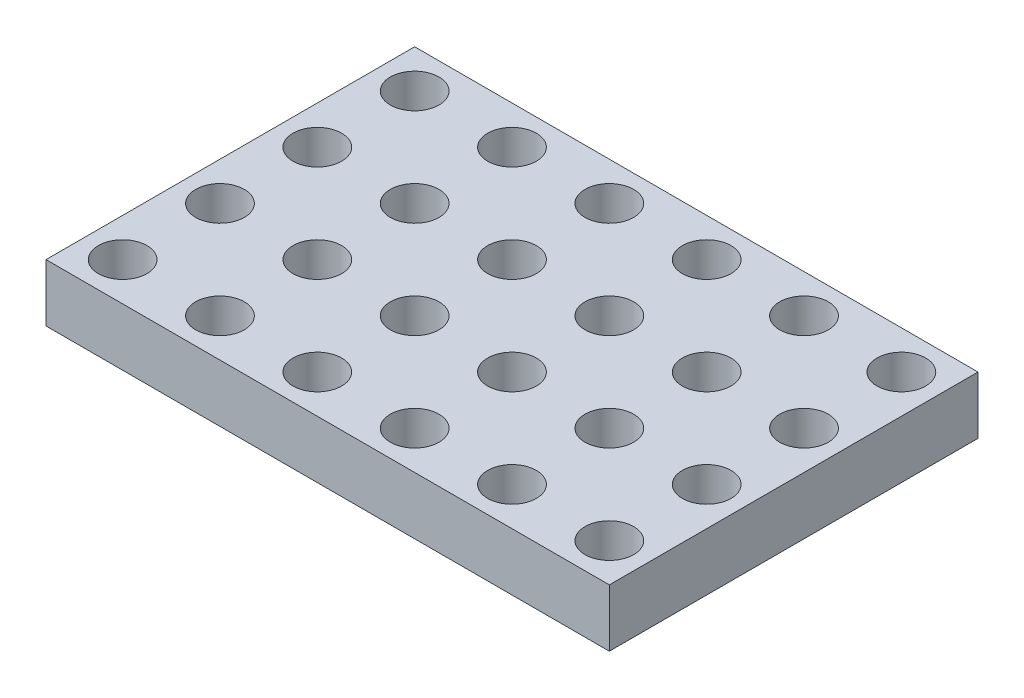
SolidWorks part; units mm, degrees
ref_plane "Front Plane" through (0, 0, 0) normal (0, 0, 1) x (1, 0, 0)
ref_plane "Top Plane" through (0, 0, 0) normal (0, 1, 0) x (1, 0, 0)
ref_plane "Right Plane" through (0, 0, 0) normal (1, 0, 0) x (0, 0, -1)
sketch "Sketch1" plane through (0, 0, 0) normal (0, 1, 0) x (1, 0, 0)
  line L0 (0, 10.1825) -> (0, -8.1829) construction
  line L1 (7.35, -4.81) -> (-7.35, -4.81)
  line L2 (7.35, -4.81) -> (7.35, 4.81)
  line L3 (7.35, 4.81) -> (-7.35, 4.81)
  line L4 (-7.35, -4.81) -> (-7.35, 4.81)
  line L5 (7.35, -4.81) -> (-7.35, 4.81) construction
  line L6 (7.35, 4.81) -> (-7.35, -4.81) construction
  line L7 (12.6443, 0) -> (-13.0323, 0) construction
  circle A0 centre (-6.35, 3.81) radius 0.635
  circle A1 centre (-3.81, 3.81) radius 0.635
  circle A2 centre (-1.27, 3.81) radius 0.635
  circle A3 centre (1.27, 3.81) radius 0.635
  circle A4 centre (3.81, 3.81) radius 0.635
  circle A5 centre (6.35, 3.81) radius 0.635
  circle A8 centre (-6.35, 1.27) radius 0.635
  circle A9 centre (-3.81, 1.27) radius 0.635
  circle A10 centre (-1.27, 1.27) radius 0.635
  circle A11 centre (1.27, 1.27) radius 0.635
  circle A12 centre (3.81, 1.27) radius 0.635
  circle A13 centre (6.35, 1.27) radius 0.635
  circle A16 centre (-6.35, -1.27) radius 0.635
  circle A17 centre (-3.81, -1.27) radius 0.635
  circle A18 centre (-1.27, -1.27) radius 0.635
  circle A19 centre (1.27, -1.27) radius 0.635
  circle A20 centre (3.81, -1.27) radius 0.635
  circle A21 centre (6.35, -1.27) radius 0.635
  circle A24 centre (-6.35, -3.81) radius 0.635
  circle A25 centre (-3.81, -3.81) radius 0.635
  circle A26 centre (-1.27, -3.81) radius 0.635
  circle A27 centre (1.27, -3.81) radius 0.635
  circle A28 centre (3.81, -3.81) radius 0.635
  circle A29 centre (6.35, -3.81) radius 0.635
  point P0 (0, 0)
  dimension "D5" = 1.27
  dimension "D1" = 12.7
  dimension "D2" = 7.62
  dimension "D6" = 1
  dimension "D7" = 1
  dimension "D3" = 6
  dimension "D4" = 4
extrude "Boss-Extrude2" add sketch "Sketch1" along normal blind 1.5
equation "\"D7@Sketch1\"=\"D6@Sketch1\""
